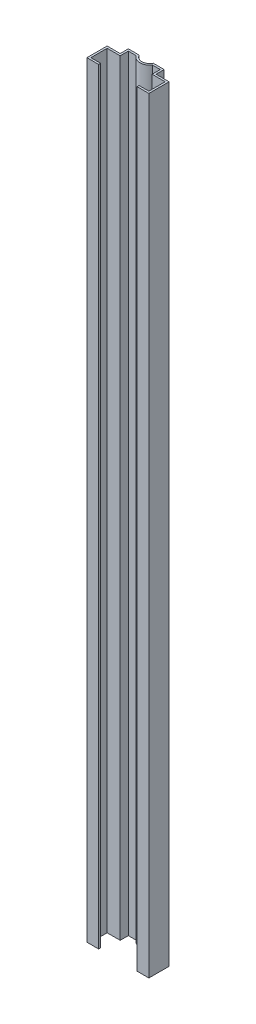
SolidWorks part; units mm, degrees
ref_plane "Front Plane" through (0, 0, 0) normal (0, 0, 1) x (1, 0, 0)
ref_plane "Top Plane" through (0, 0, 0) normal (0, 1, 0) x (1, 0, 0)
ref_plane "Right Plane" through (0, 0, 0) normal (1, 0, 0) x (0, 0, -1)
ref_plane "Plane1" through (0, 2350, 0) normal (0, 1, 0) x (1, 0, 0)
sketch "Sketch1" plane through (0, 2350, 0) normal (0, 1, 0) x (1, 0, 0)
  line L0 (25, 75) -> (49, 75)
  line L1 (49, 75) -> (49, 50)
  line L2 (49, 50) -> (89, 50)
  line L3 (89, 50) -> (89, 0)
  line L4 (89, 0) -> (59, 0)
  line L5 (59, 0) -> (59, -6)
  line L6 (59, -6) -> (95, -6)
  line L7 (95, -6) -> (95, 56)
  line L8 (95, 56) -> (55, 56)
  line L9 (55, 56) -> (55, 81)
  line L10 (55, 81) -> (21.5406, 81)
  line L11 (-21.5406, 81) -> (-55, 81)
  line L12 (-55, 81) -> (-55, 56)
  line L13 (-55, 56) -> (-95, 56)
  line L14 (-95, 56) -> (-95, -6)
  line L15 (-95, -6) -> (-59, -6)
  line L16 (-59, -6) -> (-59, 0)
  line L17 (-59, 0) -> (-89, 0)
  line L18 (-89, 0) -> (-89, 50)
  line L19 (-89, 50) -> (-49, 50)
  line L20 (-49, 50) -> (-49, 75)
  line L21 (-49, 75) -> (-25, 75)
  arc A0 (-25, 75) -> (25, 75) centre (0, 91.5831) ccw
  arc A1 (21.5406, 81) -> (-21.5406, 81) centre (0, 91.5831) cw
extrude "Boss-Extrude1" add sketch "Sketch1" against normal blind 2350
